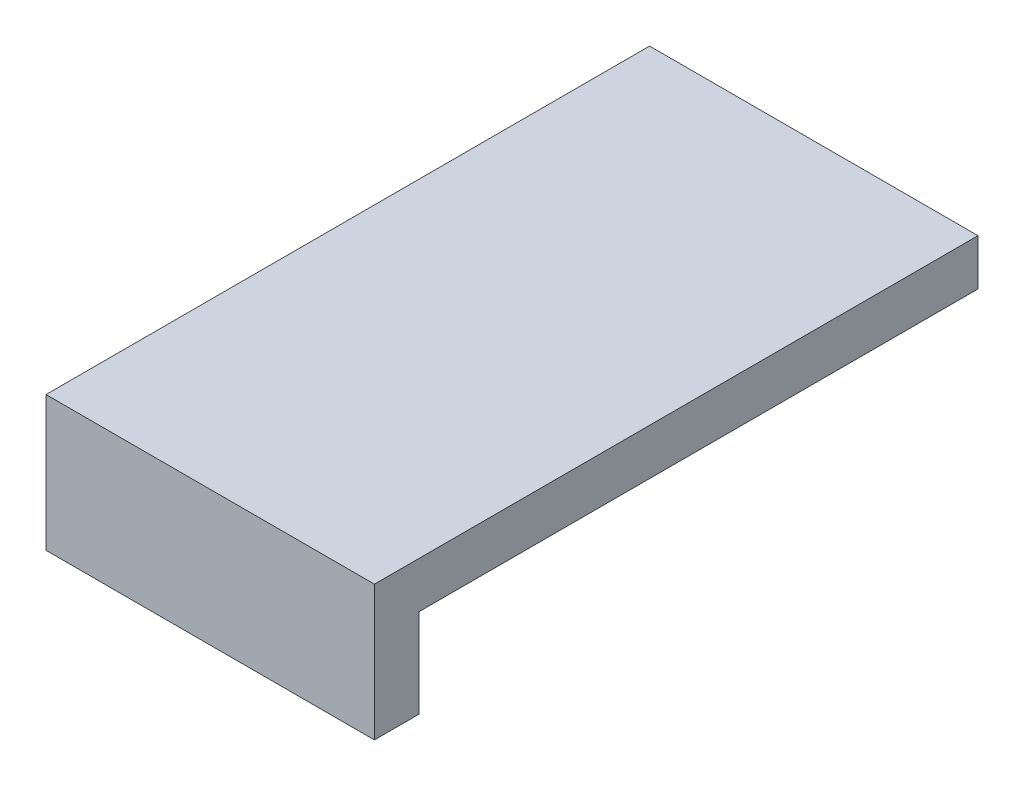
SolidWorks part; units mm, degrees
ref_plane "Front Plane" through (0, 0, 0) normal (0, 0, 1) x (1, 0, 0)
ref_plane "Top Plane" through (0, 0, 0) normal (0, 1, 0) x (1, 0, 0)
ref_plane "Right Plane" through (0, 0, 0) normal (1, 0, 0) x (0, 0, -1)
sketch "Sketch1" plane through (0, 0, 0) normal (0, 1, 0) x (1, 0, 0)
  line L1 (-9.25, -17) -> (9.25, -17)
  line L2 (-9.25, -17) -> (-9.25, 17)
  line L3 (-9.25, 17) -> (9.25, 17)
  line L4 (9.25, -17) -> (9.25, 17)
  line L5 (-9.25, -17) -> (9.25, 17) construction
  line L6 (-9.25, 17) -> (9.25, -17) construction
  point P0 (0, 0)
  dimension "D1" = 18.5
  dimension "D2" = 34
extrude "Boss-Extrude1" add sketch "Sketch1" along normal blind 2.6
sketch "Sketch2" plane through (0, 0, 0) normal (0, -1, 0) x (1, 0, 0)
  line L0 (9.25, 17) -> (9.25, -17) construction
  line L1 (-9.25, 17) -> (9.25, 17)
  line L2 (-9.25, 17) -> (-9.25, 14.5)
  line L3 (-9.25, 14.5) -> (9.25, 14.5)
  line L4 (9.25, 17) -> (9.25, 14.5)
  dimension "D1" = 2.5
extrude "Boss-Extrude2" add sketch "Sketch2" along normal blind 5
